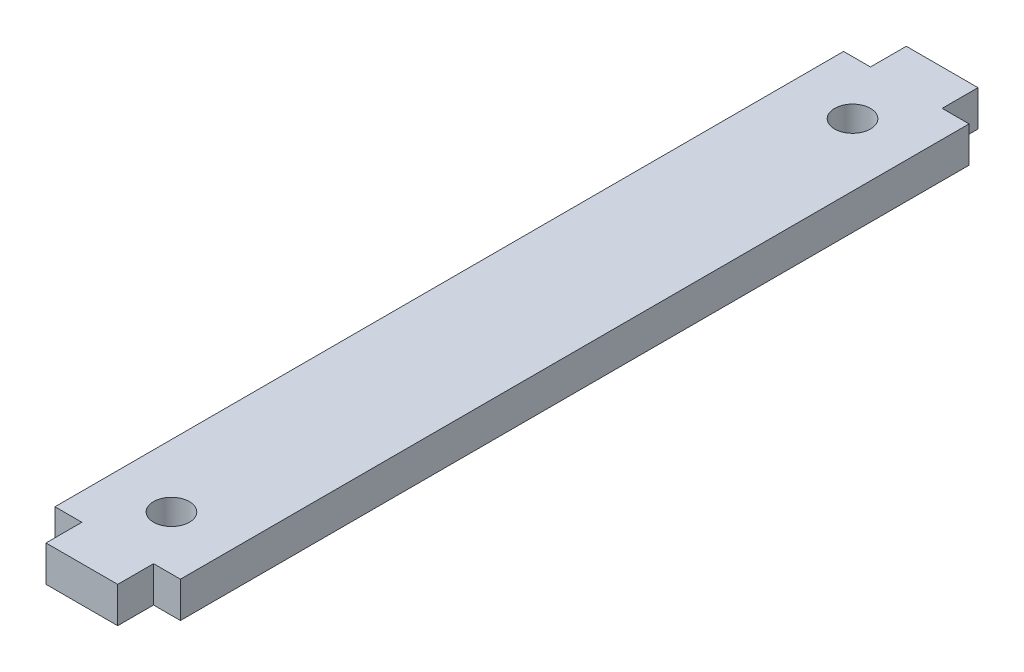
SolidWorks part; units mm, degrees
material "Beech"
ref_plane "Front Plane" through (0, 0, 0) normal (0, 0, 1) x (1, 0, 0)
ref_plane "Top Plane" through (0, 0, 0) normal (0, 1, 0) x (1, 0, 0)
ref_plane "Right Plane" through (0, 0, 0) normal (1, 0, 0) x (0, 0, -1)
sketch "Sketch1" plane through (0, 0, 0) normal (0, 1, 0) x (1, 0, 0)
  line L0 (-8.89, 0) -> (8.89, 0) construction
  line L1 (8.89, 55.88) -> (-8.89, 55.88)
  line L2 (8.89, 55.88) -> (8.89, -55.88)
  line L3 (8.89, -55.88) -> (-8.89, -55.88)
  line L4 (-8.89, 55.88) -> (-8.89, -55.88)
  line L5 (8.89, 55.88) -> (-8.89, -55.88) construction
  line L6 (8.89, -55.88) -> (-8.89, 55.88) construction
  line L7 (-5.08, 55.88) -> (5.08, 55.88)
  line L8 (-5.08, 55.88) -> (-5.08, 60.96)
  line L9 (-5.08, 60.96) -> (5.08, 60.96)
  line L10 (5.08, 55.88) -> (5.08, 60.96)
  line L11 (-5.08, 55.88) -> (5.08, 60.96) construction
  line L12 (-5.08, 60.96) -> (5.08, 55.88) construction
  line L13 (-5.08, -60.96) -> (5.08, -55.88) construction
  line L14 (-5.08, -55.88) -> (5.08, -60.96) construction
  line L15 (5.08, -55.88) -> (5.08, -60.96)
  line L16 (-5.08, -60.96) -> (5.08, -60.96)
  line L17 (-5.08, -55.88) -> (-5.08, -60.96)
  line L18 (-5.08, -55.88) -> (5.08, -55.88)
  line L19 (0, 55.88) -> (0, 48.26) construction
  circle A0 centre (0, 48.26) radius 2.54
  circle A1 centre (0, -48.26) radius 2.54
  point P0 (0, 0)
  point P10 (0, 58.42)
  point P17 (0, -58.42)
  dimension "D6" = 5.08
  dimension "D1" = 17.78
  dimension "D2" = 111.76
  dimension "D3" = 10.16
  dimension "D4" = 3.81
  dimension "D5" = 5.08
  dimension "D7" = 7.62
extrude "Boss-Extrude1" add sketch "Sketch1" along normal blind 5.08 contours L1 L4 L3 L2 | L3 L17 L16 L15 | L1 L10 L9 L8
